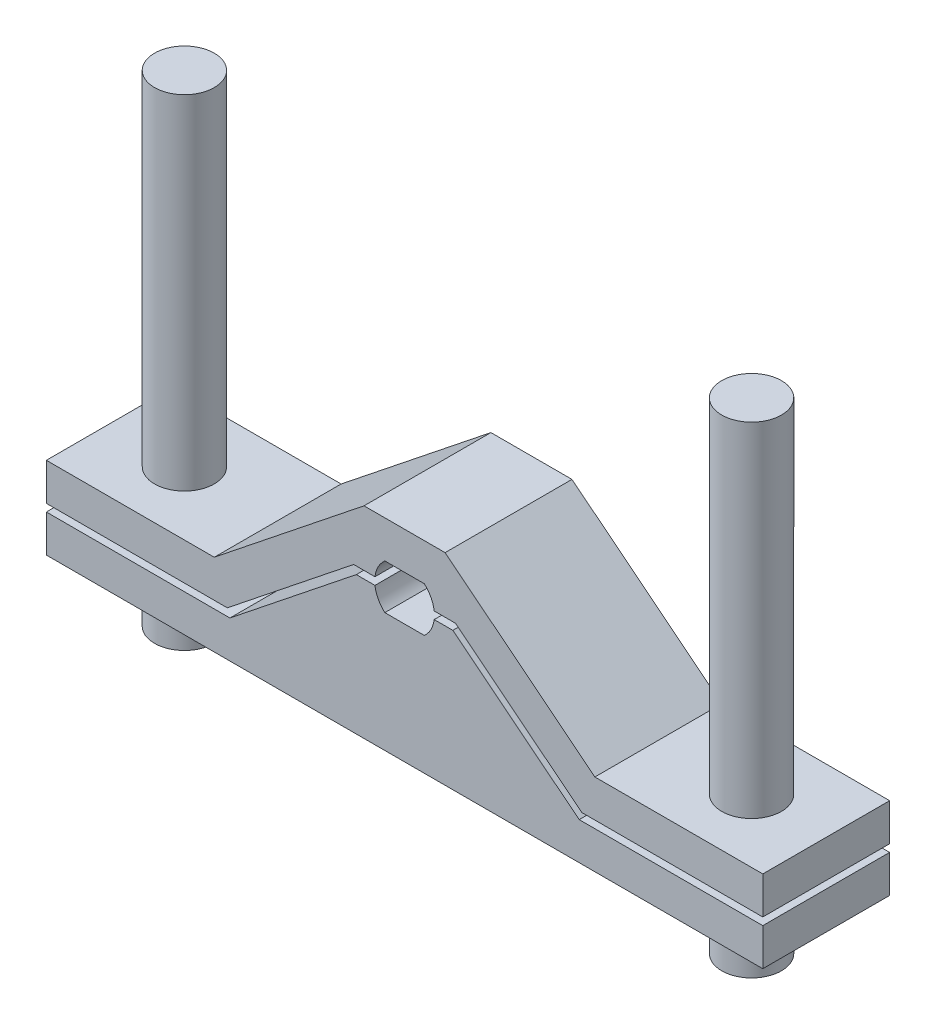
SolidWorks part; units mm, degrees
material "AISI 1020"
ref_plane "Спереди" through (0, 0, 0) normal (0, 0, 1) x (1, 0, 0)
ref_plane "Сверху" through (0, 0, 0) normal (0, 1, 0) x (1, 0, 0)
ref_plane "Справа" through (0, 0, 0) normal (1, 0, 0) x (0, 0, -1)
sketch "Эскиз2" plane through (0, 0, 0) normal (0, 0, 1) x (1, 0, 0)
  line L0 (-1000, 0) -> (49000, 0) construction
  line L1 (0, -1000) -> (0, 49000) construction
  line L2 (-5.2915, 6) -> (5.2915, 6) construction
  line L3 (5.2915, -6) -> (-5.2915, -6) construction
  line L4 (-5.2915, 6) -> (0, 6)
  line L5 (0, -6) -> (-5.2915, -6)
  line L6 (0, -6) -> (0, -38)
  line L7 (0, -38) -> (-96, -38)
  line L8 (-96, -38) -> (-96, -28)
  line L9 (-96, -28) -> (-46.8018, -28)
  line L10 (-46.8018, -28) -> (-12.9373, -1)
  line L11 (-12.9373, -1) -> (-7.9373, -1)
  line L12 (0, 6) -> (0, 16)
  line L13 (0, 16) -> (-10.8643, 16)
  line L14 (-10.8643, 16) -> (-51, -16)
  line L15 (-51, -16) -> (-96, -16)
  line L16 (-96, -16) -> (-96, -26)
  line L17 (-96, -26) -> (-47.5015, -26)
  line L18 (-47.5015, -26) -> (-13.637, 1)
  line L19 (-13.637, 1) -> (-7.9373, 1)
  arc A0 (-5.2915, 6) -> (-5.2915, -6) centre (0, 0) ccw construction
  arc A2 (-5.2915, 6) -> (-7.9373, 1) centre (0, 0) ccw
  circle A4 centre (0, 0) radius 53 construction
  circle A5 centre (0, 0) radius 100 construction
  arc A6 (-7.9373, -1) -> (-5.2915, -6) centre (0, 0) ccw
  dimension "D1" = 1
  dimension "D2" = 5
  dimension "D3" = 10
  dimension "D4" = 15
  dimension "D5" = 45
  dimension "D6" = 1
  dimension "D7" = 2
  dimension "D8" = 2
  dimension "D9" = 10
  dimension "D10" = 10
extrude "Бобышка-Вытянуть1" add sketch "Эскиз2" against normal up to surface (34 mm away)
sketch "Эскиз3" plane through (0, -16, 0) normal (0, 1, 0) x (1, 0, 0)
  circle A0 centre (-76, 17) radius 8 construction
  circle A1 centre (-76, 17) radius 8
extrude "Бобышка-Вытянуть2" add sketch "Эскиз3" along normal offset from surface 20 and the other way offset from surface (37 mm away) 15 other way up to face at (-48, -38, -17)
cosmetic thread "Условное изображение резьбы1" parameters "D1"=15, "D2"=14.344
cosmetic thread "Условное изображение резьбы2" parameters "D1"=15, "D2"=14.344
sketch "Эскиз4" plane through (0, -38, 0) normal (0, -1, 0) x (1, 0, 0)
  circle A2 centre (-76, -17) radius 8.5
  circle A3 centre (-76, -17) radius 8.5
  dimension "D1" = 0.5
extrude "Вырез-Вытянуть1" cut sketch "Эскиз4" against normal up to surface (10 mm away) up to face at (-71.4009, -28, -17)
mirror "Зеркальное отражение1" about plane through (0, -6, -138.7855) normal (1, 0, 0) of bodies 106 105
other "Сохранить тела1"
